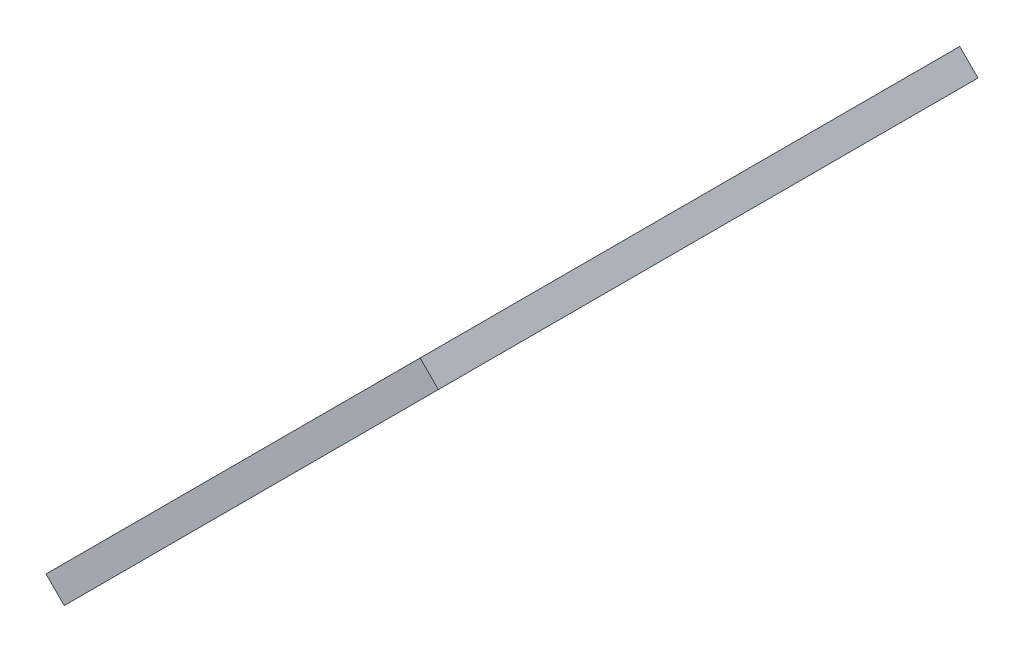
SolidWorks part; units mm, degrees
material "Acrylic (Medium-high impact)"
ref_plane "Front Plane" through (0, 0, 0) normal (0, 0, 1) x (1, 0, 0)
ref_plane "Top Plane" through (0, 0, 0) normal (0, 1, 0) x (1, 0, 0)
ref_plane "Right Plane" through (0, 0, 0) normal (1, 0, 0) x (0, 0, -1)
ref_plane "Plane2" through (80.4015, -80.4015, 0) normal (0.7071, -0.7071, 0) x (-0.7071, -0.7071, 0)
sketch "Sketch2" plane through (80.4015, -80.4015, 0) normal (0.7071, -0.7071, 0) x (-0.7071, -0.7071, 0)
  line L0 (49.6381, -111.1649) -> (111.1649, -111.1649) construction
  line L1 (49.6381, -48.4129) -> (49.6381, -111.1649) construction
  line L2 (111.1649, -111.1649) -> (111.1649, -4.9069) construction
  line L3 (111.1649, -4.9069) -> (49.6381, -48.4129) construction
  line L4 (49.6381, -111.1649) -> (111.1649, -111.1649)
  line L5 (49.6381, -48.4129) -> (49.6381, -111.1649)
  line L6 (111.1649, -111.1649) -> (111.1649, -4.9069)
  line L7 (111.1649, -4.9069) -> (49.6381, -48.4129)
extrude "Boss-Extrude2" add sketch "Sketch2" against normal mid plane 3
